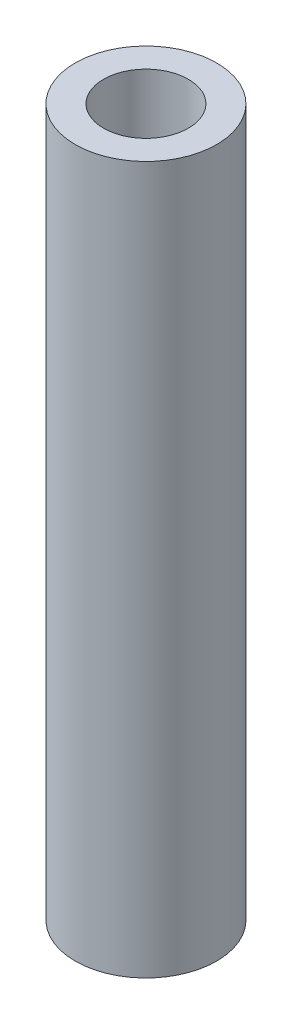
SolidWorks part; units mm, degrees
material "6061 Alloy"
ref_plane "Front Plane" through (0, 0, 0) normal (0, 0, 1) x (1, 0, 0)
ref_plane "Top Plane" through (0, 0, 0) normal (0, 1, 0) x (1, 0, 0)
ref_plane "Right Plane" through (0, 0, 0) normal (1, 0, 0) x (0, 0, -1)
sketch "Sketch1" plane through (0, 0, 0) normal (0, 1, 0) x (1, 0, 0)
  circle A0 centre (0, 0) radius 1.5
  circle A1 centre (0, 0) radius 2.5
  dimension "D1" = 3
  dimension "D2" = 5
extrude "Boss-Extrude1" add sketch "Sketch1" along normal blind 25
